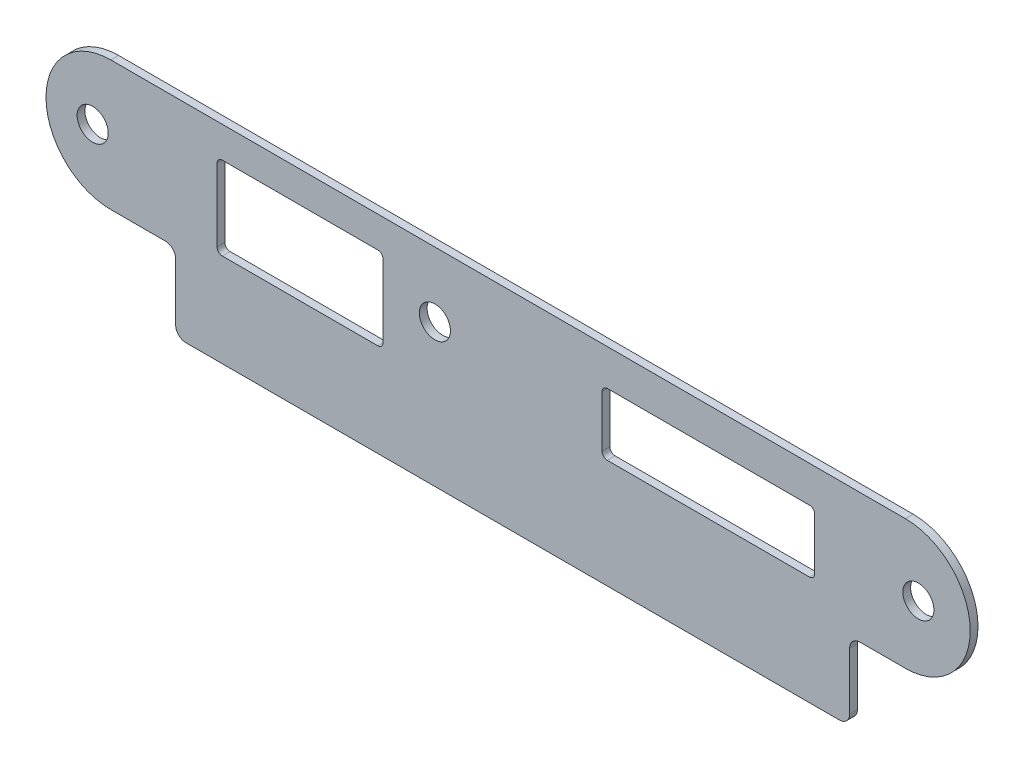
SolidWorks part; units mm, degrees
ref_plane "Plan de face" through (0, 0, 0) normal (0, 0, 1) x (1, 0, 0)
ref_plane "Plan de dessus" through (0, 0, 0) normal (0, 1, 0) x (1, 0, 0)
ref_plane "Plan de droite" through (0, 0, 0) normal (1, 0, 0) x (0, 0, -1)
sketch "Esquisse1" plane through (0, 0, 0) normal (0, 0, 1) x (1, 0, 0)
  line L0 (-31.5, 13) -> (-61.5, 13) construction
  line L1 (-30.5, -2) -> (-30.5, 12) construction
  line L2 (-61.5, -3) -> (-31.5, -3) construction
  line L3 (-62.5, 12) -> (-62.5, -2) construction
  line L4 (-31.5, 13) -> (-61.5, 13)
  line L5 (-30.5, -2) -> (-30.5, 12)
  line L6 (-83, -6) -> (-72.5, -6)
  line L7 (-70.5, -8) -> (-70.5, -19)
  line L8 (-68.5, -21) -> (57.5, -21)
  line L9 (59.5, -19) -> (59.5, -8)
  line L10 (61.5, -6) -> (70.25, -6)
  line L11 (70.25, 19) -> (-83, 19)
  line L12 (-83, -6) -> (-72.5, -6)
  line L13 (-70.5, -8) -> (-70.5, -19)
  line L14 (-68.5, -21) -> (57.5, -21)
  line L15 (59.5, -19) -> (59.5, -8)
  line L16 (61.5, -6) -> (70.25, -6)
  line L17 (70.25, 19) -> (-83, 19)
  line L18 (-61.5, -3) -> (-31.5, -3)
  line L19 (-62.5, 12) -> (-62.5, -2)
  line L20 (51.75, 12) -> (12.75, 12) construction
  line L21 (11.75, 11) -> (11.75, 1) construction
  line L22 (12.75, 0) -> (51.75, 0) construction
  line L23 (52.75, 1) -> (52.75, 11) construction
  line L24 (51.75, 12) -> (12.75, 12)
  line L25 (11.75, 11) -> (11.75, 1)
  line L26 (12.75, 0) -> (51.75, 0)
  line L27 (52.75, 1) -> (52.75, 11)
  circle A0 centre (-86.5, 6.5) radius 3 construction
  circle A1 centre (-86.5, 6.5) radius 3
  arc A2 (-61.5, 13) -> (-62.5, 12) centre (-61.5, 12) ccw construction
  arc A3 (-30.5, 12) -> (-31.5, 13) centre (-31.5, 12) ccw construction
  arc A4 (-31.5, -3) -> (-30.5, -2) centre (-31.5, -2) ccw construction
  arc A5 (-62.5, -2) -> (-61.5, -3) centre (-61.5, -2) ccw construction
  arc A6 (-83, 19) -> (-83, -6) centre (-83, 6.5) ccw
  arc A7 (-70.5, -8) -> (-72.5, -6) centre (-72.5, -8) ccw
  arc A8 (-70.5, -19) -> (-68.5, -21) centre (-68.5, -19) ccw
  arc A9 (57.5, -21) -> (59.5, -19) centre (57.5, -19) ccw
  arc A10 (61.5, -6) -> (59.5, -8) centre (61.5, -8) ccw
  arc A11 (70.25, -6) -> (70.25, 19) centre (70.25, 6.5) ccw
  arc A12 (-83, 19) -> (-83, -6) centre (-83, 6.5) ccw
  arc A13 (-70.5, -8) -> (-72.5, -6) centre (-72.5, -8) ccw
  arc A14 (-70.5, -19) -> (-68.5, -21) centre (-68.5, -19) ccw
  arc A15 (57.5, -21) -> (59.5, -19) centre (57.5, -19) ccw
  arc A16 (61.5, -6) -> (59.5, -8) centre (61.5, -8) ccw
  arc A17 (70.25, -6) -> (70.25, 19) centre (70.25, 6.5) ccw
  arc A18 (-61.5, 13) -> (-62.5, 12) centre (-61.5, 12) ccw
  arc A19 (-30.5, 12) -> (-31.5, 13) centre (-31.5, 12) ccw
  arc A20 (-31.5, -3) -> (-30.5, -2) centre (-31.5, -2) ccw
  arc A21 (-62.5, -2) -> (-61.5, -3) centre (-61.5, -2) ccw
  circle A22 centre (-20.5, 6.5) radius 3 construction
  circle A23 centre (-20.5, 6.5) radius 3
  arc A24 (52.75, 11) -> (51.75, 12) centre (51.75, 11) ccw construction
  arc A25 (12.75, 12) -> (11.75, 11) centre (12.75, 11) ccw construction
  arc A26 (11.75, 1) -> (12.75, 0) centre (12.75, 1) ccw construction
  arc A27 (51.75, 0) -> (52.75, 1) centre (51.75, 1) ccw construction
  arc A28 (52.75, 11) -> (51.75, 12) centre (51.75, 11) ccw
  arc A29 (12.75, 12) -> (11.75, 11) centre (12.75, 11) ccw
  arc A30 (11.75, 1) -> (12.75, 0) centre (12.75, 1) ccw
  arc A31 (51.75, 0) -> (52.75, 1) centre (51.75, 1) ccw
  circle A32 centre (72.75, 6.5) radius 3 construction
  circle A33 centre (72.75, 6.5) radius 3
  dimension "D1" = 0
extrude "Extrusion1" add sketch "Esquisse1" along normal blind 1.5
